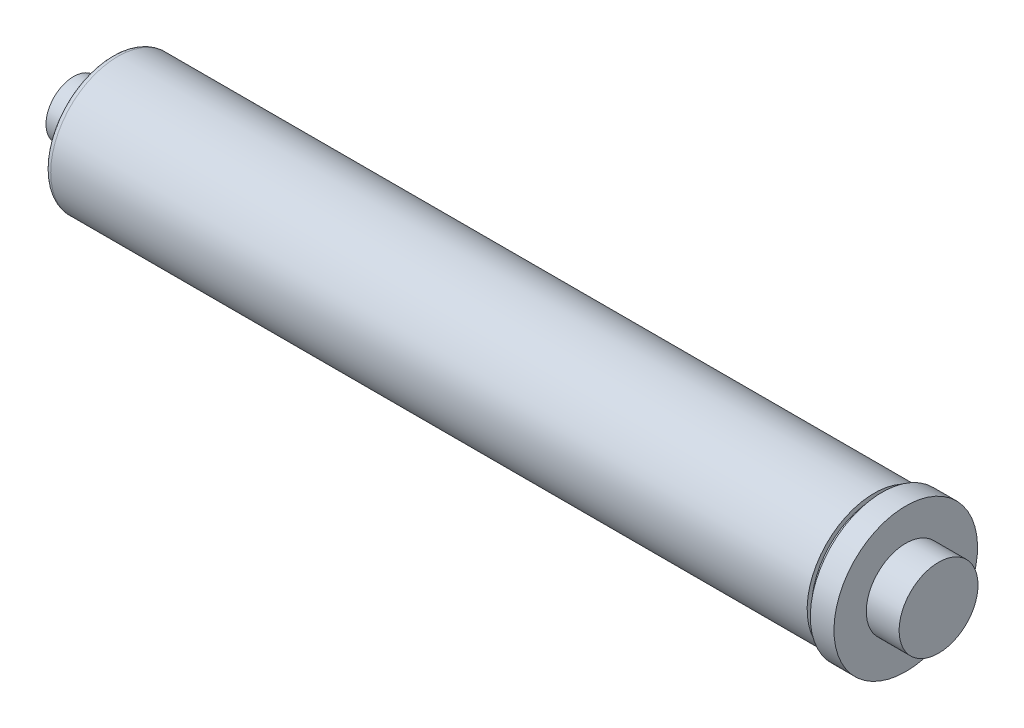
SolidWorks part; units mm, degrees
material "6061-T6 (SS)"
ref_plane "Front Plane" through (0, 0, 0) normal (0, 0, 1) x (1, 0, 0)
ref_plane "Top Plane" through (0, 0, 0) normal (0, 1, 0) x (1, 0, 0)
ref_plane "Right Plane" through (0, 0, 0) normal (1, 0, 0) x (0, 0, -1)
sketch "Sketch1" plane through (0, 0, 0) normal (0, 0, 1) x (1, 0, 0)
  line L0 (0, 0) -> (0, 11.1125)
  line L1 (0, 11.1125) -> (15.24, 11.1125)
  line L2 (15.24, 11.1125) -> (15.24, 26.9875)
  line L3 (15.24, 26.9875) -> (322.199, 26.9875)
  line L4 (322.199, 26.9875) -> (322.199, 25.1714)
  line L5 (322.199, 25.1714) -> (325.374, 25.1714)
  line L6 (325.374, 25.1714) -> (325.374, 28.8925)
  line L7 (325.374, 28.8925) -> (334.899, 28.8925)
  line L8 (334.899, 28.8925) -> (334.899, 15.875)
  line L9 (334.899, 15.875) -> (348.107, 15.875)
  line L10 (348.107, 15.875) -> (348.107, 0)
  line L11 (348.107, 0) -> (0, 0)
  line L12 (0, 0) -> (452.3115, 0) construction
  dimension "D1" = 310.134
  dimension "D2" = 15.24
  dimension "D3" = 3.175
  dimension "D4" = 9.525
  dimension "D5" = 13.208
  dimension "D6" = 15.875
  dimension "D7" = 28.8925
  dimension "D8" = 26.9875
  dimension "D9" = 11.1125
  dimension "D10" = 25.1714
revolve "Revolve1" add sketch "Sketch1" angle 360 about L12
fillet "Fillet1" radius 2.54 1 edges at (15.24, -26.9875, 0)
sketch "Sketch2" plane through (0, 0, 0) normal (-1, 0, 0) x (0, 0, 1)
  circle A1 centre (0, 0) radius 7.9375
  dimension "D1" = 15.875
extrude "Cut-Extrude1" cut sketch "Sketch2" against normal blind 6.35
sketch "Sketch3" plane through (6.35, 0, 0) normal (-1, 0, 0) x (0, 0, 1)
  circle A0 centre (0, 0) radius 1.5875
  dimension "D1" = 3.175
extrude "Cut-Extrude2" cut sketch "Sketch3" against normal blind 6.35
